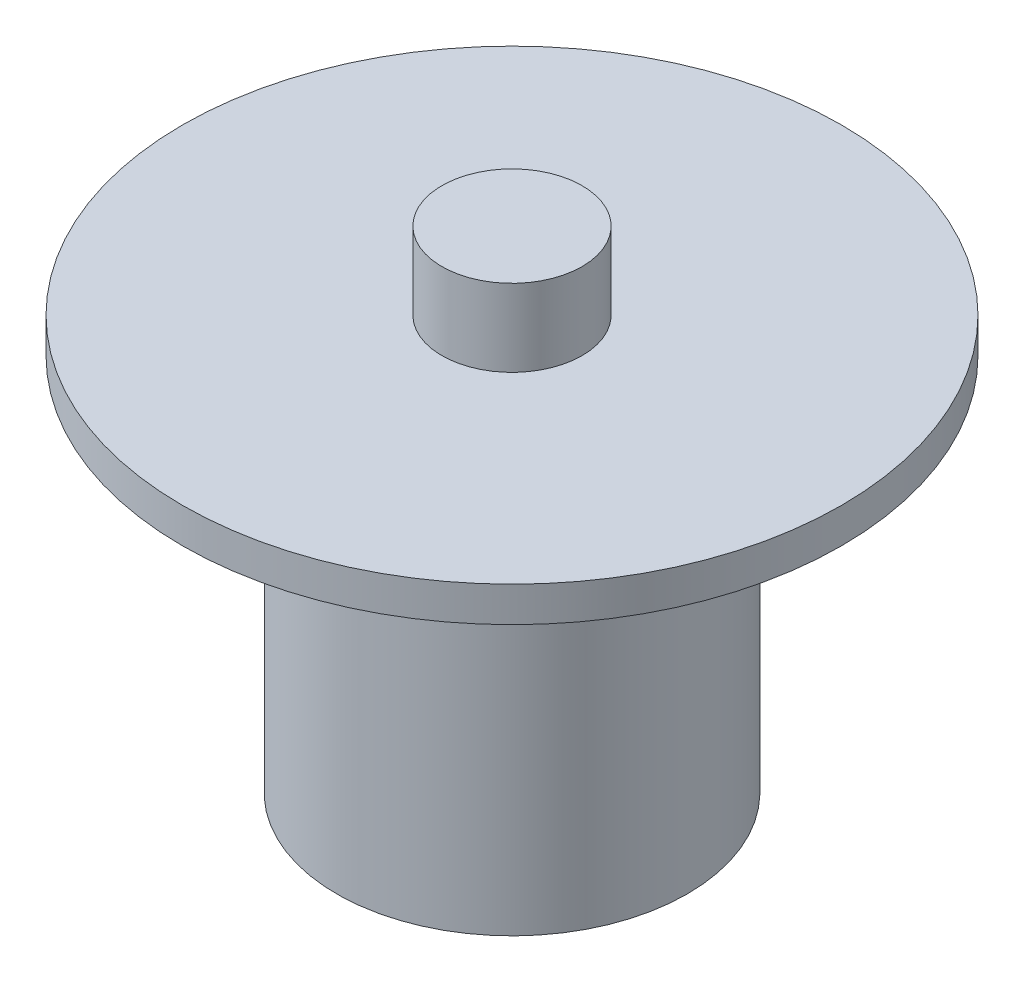
SolidWorks part; units mm, degrees
ref_plane "Front Plane" through (0, 0, 0) normal (0, 0, 1) x (1, 0, 0)
ref_plane "Top Plane" through (0, 0, 0) normal (0, 1, 0) x (1, 0, 0)
ref_plane "Right Plane" through (0, 0, 0) normal (1, 0, 0) x (0, 0, -1)
sketch "Sketch1" plane through (0, 0, 0) normal (0, 0, 1) x (1, 0, 0)
  line L0 (0, -8.75) -> (0, 8.75)
  line L1 (0, 8.75) -> (-2.5, 8.75)
  line L2 (-2.5, 8.75) -> (-2.5, 6)
  line L3 (-2.5, 6) -> (-11.75, 6)
  line L4 (-11.75, 6) -> (-11.75, 4.75)
  line L5 (-11.75, 4.75) -> (-6.25, 4.75)
  line L6 (-6.25, 4.75) -> (-6.25, -8.75)
  line L7 (-6.25, -8.75) -> (0, -8.75)
  point P4 (0, 0)
  dimension "D1" = 6.25
  dimension "D2" = 11.75
  dimension "D3" = 17.5
  dimension "D4" = 2.5
  dimension "D5" = 1.25
  dimension "D6" = 13.5
revolve "Revolve1" add sketch "Sketch1" angle 360 about L0
